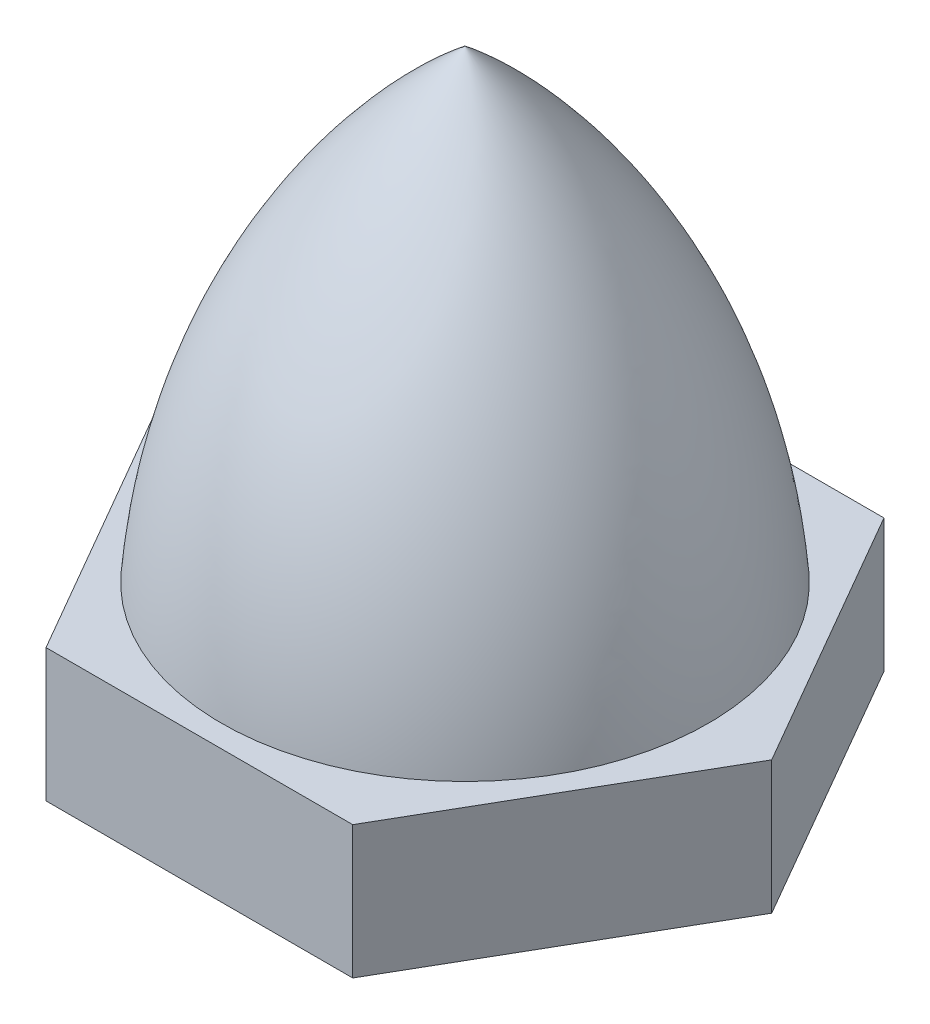
SolidWorks part; units mm, degrees
ref_plane "Ön Düzlem" through (0, 0, 0) normal (0, 0, 1) x (1, 0, 0)
ref_plane "Üst Düzlem" through (0, 0, 0) normal (0, 1, 0) x (1, 0, 0)
ref_plane "Sağ Düzlem" through (0, 0, 0) normal (1, 0, 0) x (0, 0, -1)
sketch "Çizim1" plane through (0, 0, 0) normal (0, 0, 1) x (1, 0, 0)
  line L0 (11.079, 25.3986) -> (11.079, 14.8986)
  line L1 (11.079, 14.8986) -> (16.579, 14.8986)
  arc A0 (16.579, 14.8986) -> (11.079, 25.3986) centre (1.6226, 13.7548) ccw
revolve "Döndür1" add sketch "Çizim1" angle 360 about L0
sketch "Çizim2" plane through (0, 14.8986, 0) normal (0, -1, 0) x (1, 0, 0)
  line L1 (14.5431, 6) -> (7.6149, 6)
  line L2 (7.6149, 6) -> (4.1508, 0)
  line L3 (4.1508, 0) -> (7.6149, -6)
  line L4 (7.6149, -6) -> (14.5431, -6)
  line L5 (14.5431, -6) -> (18.0072, 0)
  line L6 (18.0072, 0) -> (14.5431, 6)
  circle A0 centre (11.079, 0) radius 6 construction
  dimension "D1" = 12
extrude "Yükseklik-Ekstrüzyon1" add sketch "Çizim2" along normal blind 3
sketch "Çizim3" plane through (0, 11.8986, 0) normal (0, -1, 0) x (1, 0, 0)
  circle A0 centre (11.079, 0) radius 2.5
extrude "Kes-Ekstrüzyon1" cut sketch "Çizim3" against normal blind 10.5
